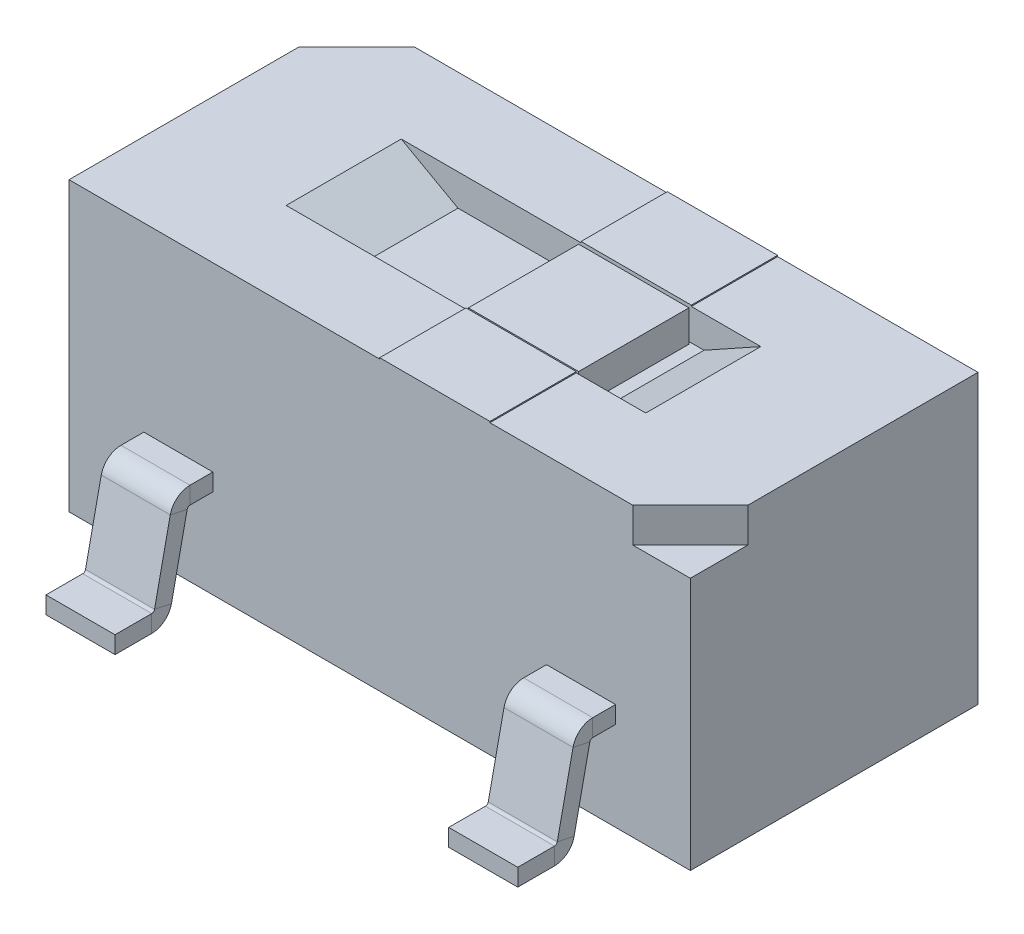
SolidWorks part; units mm, degrees
ref_plane "Front Plane" through (0, 0, 0) normal (0, 0, 1) x (1, 0, 0)
ref_plane "Top Plane" through (0, 0, 0) normal (0, 1, 0) x (1, 0, 0)
ref_plane "Right Plane" through (0, 0, 0) normal (1, 0, 0) x (0, 0, -1)
sketch "Sketch1" plane through (0, 0, 0) normal (0, 1, 0) x (1, 0, 0)
  line L1 (-2.7, -1.25) -> (2.7, -1.25)
  line L2 (-2.7, -1.25) -> (-2.7, 1.25)
  line L3 (-2.7, 1.25) -> (2.7, 1.25)
  line L4 (2.7, -1.25) -> (2.7, 1.25)
  line L5 (-2.7, -1.25) -> (2.7, 1.25) construction
  line L6 (-2.7, 1.25) -> (2.7, -1.25) construction
  point P0 (0, 0)
  dimension "D1" = 2.5
  dimension "D2" = 5.4
extrude "Boss-Extrude1" add sketch "Sketch1" along normal blind 2.5
sketch "Sketch2" plane through (0, 2.5, 0) normal (0, 1, 0) x (1, 0, 0)
  line L0 (-2.7, 1.25) -> (-2.7, 0.75)
  line L1 (-2.7, 1.25) -> (-2.7, -1.25) construction
  line L2 (-2.7, 0.75) -> (-2.2, 1.25)
  line L3 (2.7, 1.25) -> (-2.7, 1.25) construction
  line L4 (-2.2, 1.25) -> (-2.7, 1.25)
  line L5 (2.2, -1.25) -> (2.7, -1.25)
  line L6 (-2.7, -1.25) -> (2.7, -1.25) construction
  line L7 (2.7, -1.25) -> (2.7, -0.75)
  line L8 (2.7, -1.25) -> (2.7, 1.25) construction
  line L9 (2.7, -0.75) -> (2.2, -1.25)
  dimension "D1" = 45
  dimension "D2" = 0.5
  dimension "D3" = 45
  dimension "D4" = 0.5
extrude "Cut-Extrude1" cut sketch "Sketch2" against normal blind 0.3
sketch "Sketch3" plane through (0, 0, 0) normal (0, 0, 1) x (1, 0, 0)
  line L0 (0, 2.5) -> (0, 0) construction
  line L1 (1.5625, 2.5) -> (1.0693, 2.2259)
  line L4 (-1.0693, 2.2259) -> (1.0693, 2.2259)
  line L6 (-1.5625, 2.5) -> (1.5625, 2.5)
  line L8 (-1.5625, 2.5) -> (-1.0693, 2.2259)
  line L9 (-2.7, 2.5) -> (2.2, 2.5) construction
extrude "Cut-Extrude2" cut sketch "Sketch3" against normal blind 0.5 and the other way blind 0.5
sketch "Sketch4" plane through (0, 2.2259, 0) normal (0, 1, 0) x (1, 0, 0)
  line L0 (-1.0693, 0) -> (1.0693, 0) construction
  line L1 (-1.0693, -0.5) -> (-1.0693, 0.5) construction
  line L2 (1.0693, -0.5) -> (1.0693, 0.5) construction
  line L4 (0, -0.4792) -> (0.9584, -0.4792)
  line L5 (0, -0.4792) -> (0, 0.4792)
  line L6 (0, 0.4792) -> (0.9584, 0.4792)
  line L7 (0.9584, -0.4792) -> (0.9584, 0.4792)
  line L8 (0, -0.4792) -> (0.9584, 0.4792) construction
  line L9 (0, 0.4792) -> (0.9584, -0.4792) construction
  point P6 (0.4792, 0)
extrude "Boss-Extrude2" add sketch "Sketch4" along normal up to surface (0.2741 mm away) up to face at (0, 2.5, 0)
sketch "Sketch5" plane through (0, 2.5, 0) normal (0, 1, 0) x (1, 0, 0)
  line L0 (2.7, 1.25) -> (-2.2, 1.25) construction
  line L1 (0, 1.25) -> (0.9584, 1.25)
  line L2 (0, 1.25) -> (0, 0.5)
  line L3 (0, 0.5) -> (0.9584, 0.5)
  line L4 (0.9584, 1.25) -> (0.9584, 0.5)
  line L5 (0, 1.25) -> (0.9584, 0.5) construction
  line L6 (0, 0.5) -> (0.9584, 1.25) construction
  line L7 (-1.0693, 0.5) -> (1.0693, 0.5) construction
  line L8 (0.9584, 0.4792) -> (0.9584, -0.4792) construction
  line L9 (0, 0.4792) -> (0, -0.4792) construction
  line L10 (1.5625, -0.5) -> (-1.5625, -0.5) construction
  line L11 (0, -0.5) -> (0.9584, -0.5)
  line L12 (0, -0.5) -> (0, -1.25)
  line L13 (0, -1.25) -> (0.9584, -1.25)
  line L14 (0.9584, -0.5) -> (0.9584, -1.25)
  line L15 (0, -0.5) -> (0.9584, -1.25) construction
  line L16 (0, -1.25) -> (0.9584, -0.5) construction
  line L17 (-2.7, -1.25) -> (2.2, -1.25) construction
  point P4 (0.4792, 0.875)
  point P17 (0.4792, -0.875)
extrude "Boss-Extrude3" add sketch "Sketch5" along normal blind 0.01
sketch "Sketch6" plane through (0, 0, 1.25) normal (0, 0, 1) x (1, 0, 0)
  line L0 (-2.7, 0.85) -> (2.7, 0.85) construction
  line L1 (-2.7, 2.5) -> (-2.7, 0) construction
  line L2 (2.7, 2.2) -> (2.7, 0) construction
  line L3 (-2.7, 0) -> (2.7, 0) construction
  line L4 (-0.3, 0.775) -> (0.3, 0.775)
  line L5 (-0.3, 0.775) -> (-0.3, 0.925)
  line L6 (-0.3, 0.925) -> (0.3, 0.925)
  line L7 (0.3, 0.775) -> (0.3, 0.925)
  line L8 (-0.3, 0.775) -> (0.3, 0.925) construction
  line L9 (-0.3, 0.925) -> (0.3, 0.775) construction
  point P6 (0, 0.85)
  dimension "D1" = 0.15
  dimension "D2" = 0.6
  dimension "D3" = 0.85
sketch3d "3DSketch1"
  line L0 (0, 0.85, 1.25) -> (0, 0.85, 1.4486)
  line L1 (0, 0.7708, 1.5464) -> (0, 0.1292, 1.6831)
  line L2 (0, 0.05, 1.7809) -> (0, 0.05, 2.1)
  arc A0 (0, 0.85, 1.4486) -> (0, 0.7708, 1.5464) centre (0, 0.75, 1.4486) ccw
  arc A1 (0, 0.1292, 1.6831) -> (0, 0.05, 1.7809) centre (0, 0.15, 1.7809) ccw
  point P7 (0, 0.85, 1.5295)
  point P8 (0.1, 0.75, 1.4486)
  point P11 (0, 0.05, 1.7)
  point P12 (-0.1, 0.15, 1.7809)
  dimension "D4" = 0.1
  dimension "D1" = 0.8
  dimension "D2" = 0.85
  dimension "D3" = 0.4
sweep "Sweep1" add profiles "Sketch6" path "3DSketch1"
mirror "Mirror1" about plane through (0, 0, 0) normal (0, 0, 1) of "Sweep1"
pattern_linear "LPattern1" count 2 spacing 1.75 along (1, 0, 0) count 2 spacing 1.75 along (-1, 0, 0) of "Sweep1"
sketch "Sketch7" plane through (0, 0, 2.1) normal (0, 0, 1) x (1, 0, 0)
  line L0 (0.3, 0.7865) -> (-0.3, 0.7865) construction
  line L1 (-0.4488, 1.7565) -> (0.4488, 1.7565)
  line L2 (-0.4488, 1.7565) -> (-0.4488, -0.1835)
  line L3 (-0.4488, -0.1835) -> (0.4488, -0.1835)
  line L4 (0.4488, 1.7565) -> (0.4488, -0.1835)
  line L5 (-0.4488, 1.7565) -> (0.4488, -0.1835) construction
  line L6 (-0.4488, -0.1835) -> (0.4488, 1.7565) construction
  point P0 (0, 0.7865)
extrude "Cut-Extrude3" cut sketch "Sketch7" against normal up to surface (0.85 mm away) up to face at (1.75, 0.85, 1.25)
